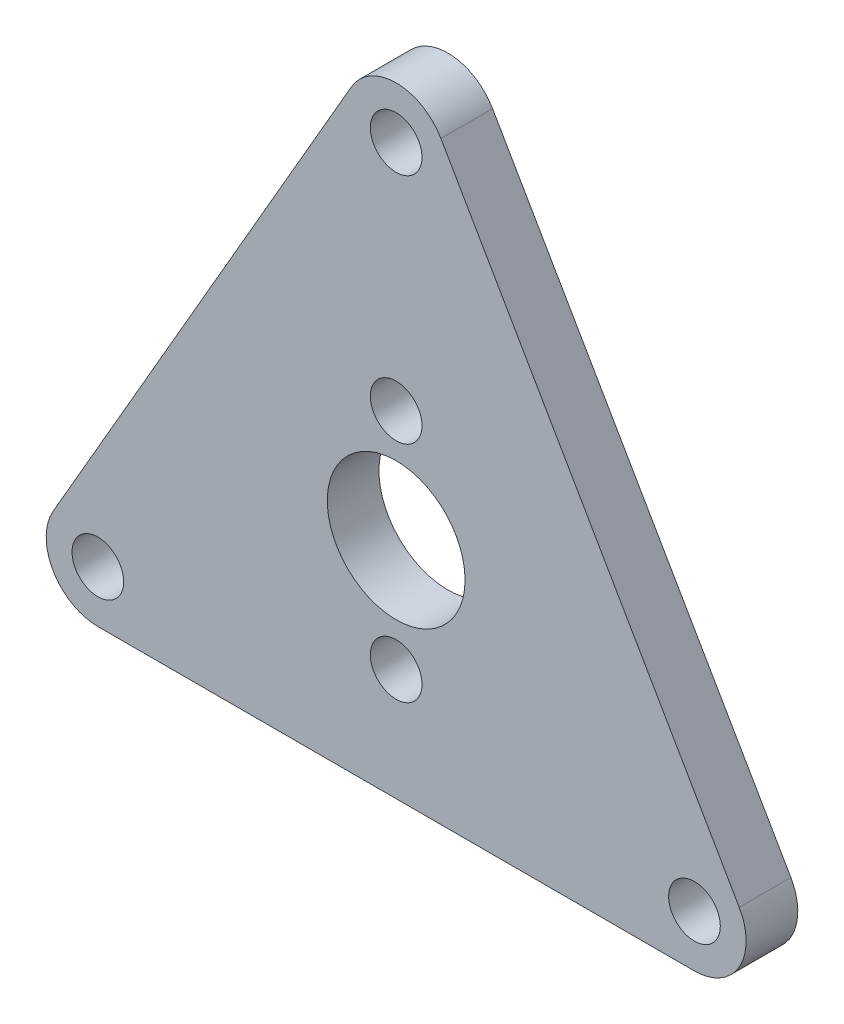
SolidWorks part; units mm, degrees
material "Thornel Mat VMA"
ref_plane "前视基准面" through (0, 0, 0) normal (0, 0, 1) x (1, 0, 0)
ref_plane "上视基准面" through (0, 0, 0) normal (0, 1, 0) x (1, 0, 0)
ref_plane "右视基准面" through (0, 0, 0) normal (1, 0, 0) x (0, 0, -1)
sketch "草图1" plane through (0, 0, 0) normal (0, 0, 1) x (1, 0, 0)
  line L0 (0, 20) -> (-17.3205, -10) construction
  line L1 (-17.3205, -10) -> (17.3205, -10) construction
  line L2 (17.3205, -10) -> (0, 20) construction
  line L3 (-2.5981, 21.5) -> (-19.9186, -8.5)
  line L4 (-17.3205, -13) -> (17.3205, -13)
  line L5 (19.9186, -8.5) -> (2.5981, 21.5)
  circle A0 centre (0, 0) radius 20 construction
  circle A1 centre (-17.3205, -10) radius 1.5
  circle A2 centre (0, 20) radius 1.5
  circle A3 centre (17.3205, -10) radius 1.5
  circle A4 centre (0, 0) radius 4
  circle A5 centre (0, 0) radius 6.5 construction
  circle A6 centre (0, 6.5) radius 1.5
  circle A7 centre (0, -6.5) radius 1.5
  circle A8 centre (0, 0) radius 26 construction
  arc A9 (-19.9186, -8.5) -> (-17.3205, -13) centre (-17.3205, -10) ccw
  arc A10 (17.3205, -13) -> (19.9186, -8.5) centre (17.3205, -10) ccw
  arc A11 (-2.5981, 21.5) -> (2.5981, 21.5) centre (0, 20) cw
  point P23 (-22.5167, -13)
  point P26 (22.5167, -13)
  point P29 (0, 26)
  dimension "D1" = 40
  dimension "D2" = 3
  dimension "D3" = 8
  dimension "D4" = 13
  dimension "D5" = 3
  dimension "D6" = 3
  dimension "D7" = 3
extrude "凸台-拉伸1" add sketch "草图1" along normal blind 3
